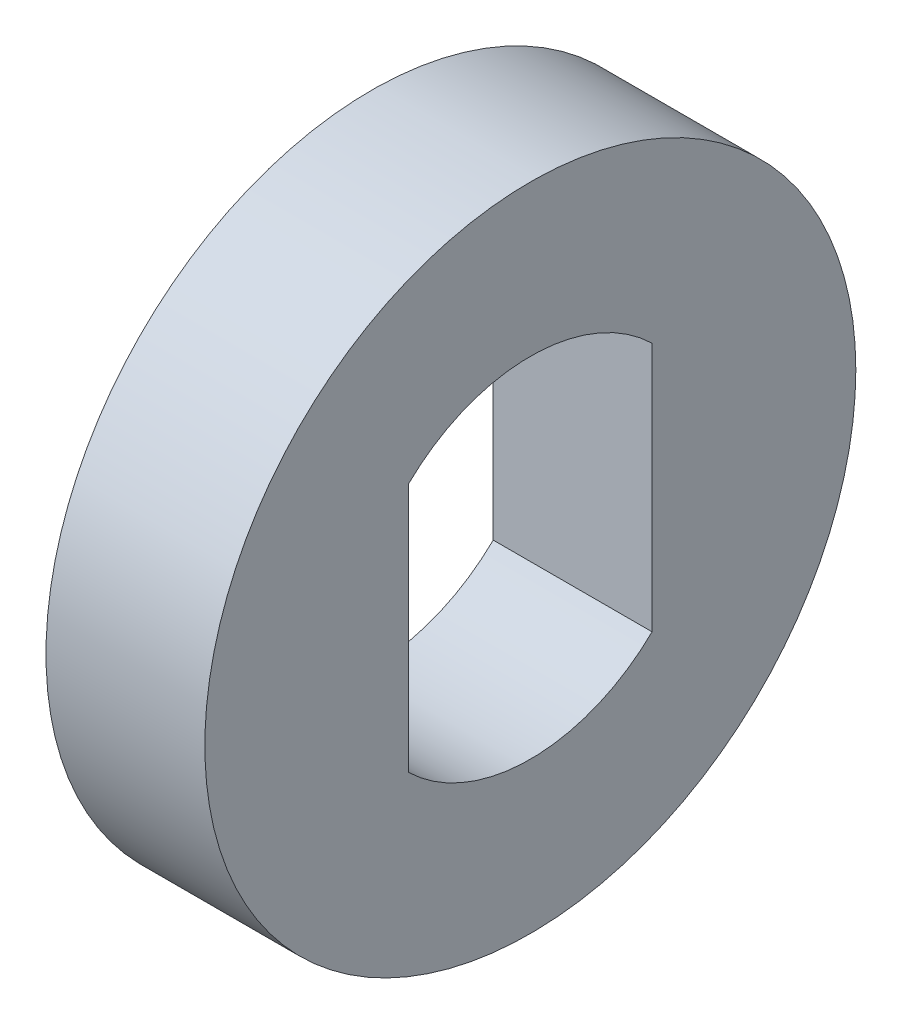
SolidWorks part; units mm, degrees
ref_plane "Alzado" through (0, 0, 0) normal (0, 0, 1) x (1, 0, 0)
ref_plane "Planta" through (0, 0, 0) normal (0, 1, 0) x (1, 0, 0)
ref_plane "Vista lateral" through (0, 0, 0) normal (1, 0, 0) x (0, 0, -1)
sketch "Croquis1" plane through (0, 0, 0) normal (1, 0, 0) x (0, 0, -1)
  line L0 (0, 2.68) -> (0, -2.68) construction
  line L1 (-1.87, 1.9198) -> (-1.87, -1.9198)
  line L2 (1.87, 1.9198) -> (1.87, -1.9198)
  line L3 (1.87, 13.8257) -> (1.87, -10.7169) construction
  line L4 (0, 13.8257) -> (0, -10.7169) construction
  line L5 (-1.87, 13.8257) -> (-1.87, -10.7169) construction
  circle A0 centre (0, 0) radius 5
  arc A1 (1.87, 1.9198) -> (-1.87, 1.9198) centre (0, 0) ccw
  arc A2 (-1.87, -1.9198) -> (1.87, -1.9198) centre (0, 0) ccw
  dimension "D1" = 10
  dimension "D2" = 5.36
  dimension "D3" = 1.87
  dimension "D4" = 1.87
extrude "Saliente-Extruir1" add sketch "Croquis1" along normal blind 2.44
